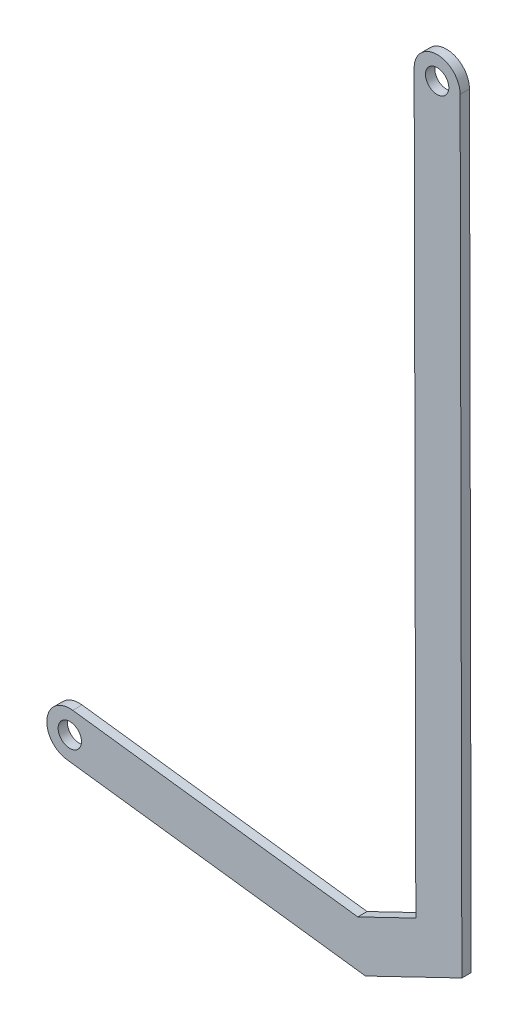
SolidWorks part; units mm, degrees
ref_plane "Front Plane" through (0, 0, 0) normal (0, 0, 1) x (1, 0, 0)
ref_plane "Top Plane" through (0, 0, 0) normal (0, 1, 0) x (1, 0, 0)
ref_plane "Right Plane" through (0, 0, 0) normal (1, 0, 0) x (0, 0, -1)
sketch "Sketch1" plane through (0, 0, 0) normal (0, 0, 1) x (1, 0, 0)
  line L3 (-0.7927, -6.2096) -> (80.4972, -16.587)
  line L4 (80.4972, -16.587) -> (106.746, -3.9314)
  line L5 (106.746, -3.9314) -> (106.2744, 204.1846)
  line L6 (0.7927, 6.2096) -> (78.4021, -3.698)
  line L7 (78.4021, -3.698) -> (94.2082, 3.9228)
  line L8 (94.2082, 3.9228) -> (93.7544, 204.1846)
  arc A0 (-0.7927, -6.2096) -> (0.7927, 6.2096) centre (0, 0) cw
  arc A1 (106.2744, 204.1846) -> (93.7544, 204.1846) centre (100.0144, 204.1846) ccw
  circle A2 centre (0, 0) radius 3.175
  circle A3 centre (100.0144, 204.1846) radius 3.175
  dimension "D3" = 6.35
  dimension "D4" = 6.35
  dimension "D2" = 81.2899
extrude "Boss-Extrude1" add sketch "Sketch1" along normal blind 2.54
